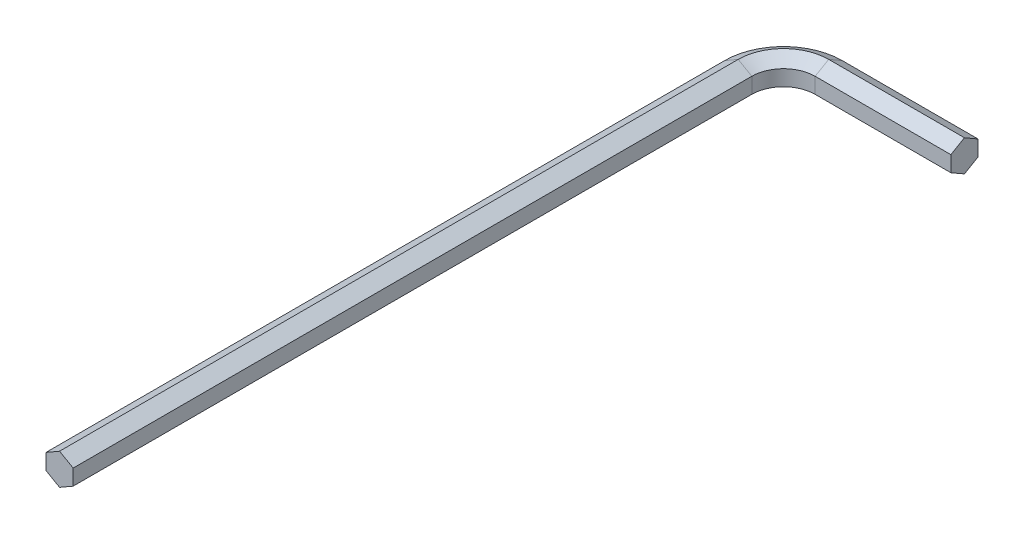
SolidWorks part; units mm, degrees
ref_plane "Front Plane" through (0, 0, 0) normal (0, 0, 1) x (1, 0, 0)
ref_plane "Top Plane" through (0, 0, 0) normal (0, 1, 0) x (1, 0, 0)
ref_plane "Right Plane" through (0, 0, 0) normal (1, 0, 0) x (0, 0, -1)
sketch "Sketch1" plane through (0, 0, 0) normal (0, 0, 1) x (1, 0, 0)
  line L1 (-1.5, 0.866) -> (-1.5, -0.866)
  line L2 (-1.5, -0.866) -> (0, -1.7321)
  line L3 (0, -1.7321) -> (1.5, -0.866)
  line L4 (1.5, -0.866) -> (1.5, 0.866)
  line L5 (1.5, 0.866) -> (0, 1.7321)
  line L6 (0, 1.7321) -> (-1.5, 0.866)
  circle A0 centre (0, 0) radius 1.5 construction
  dimension "D1" = 3
sketch "Sketch2" plane through (0, 0, 0) normal (0, 1, 0) x (1, 0, 0)
  line L0 (0, 0) -> (0, 75)
  line L1 (5, 80) -> (20, 80)
  arc A0 (0, 75) -> (5, 80) centre (5, 75) cw
  dimension "D3" = 5
  dimension "D1" = 20
  dimension "D2" = 80
sweep "Sweep1" add profiles "Sketch1" path "Sketch2"
